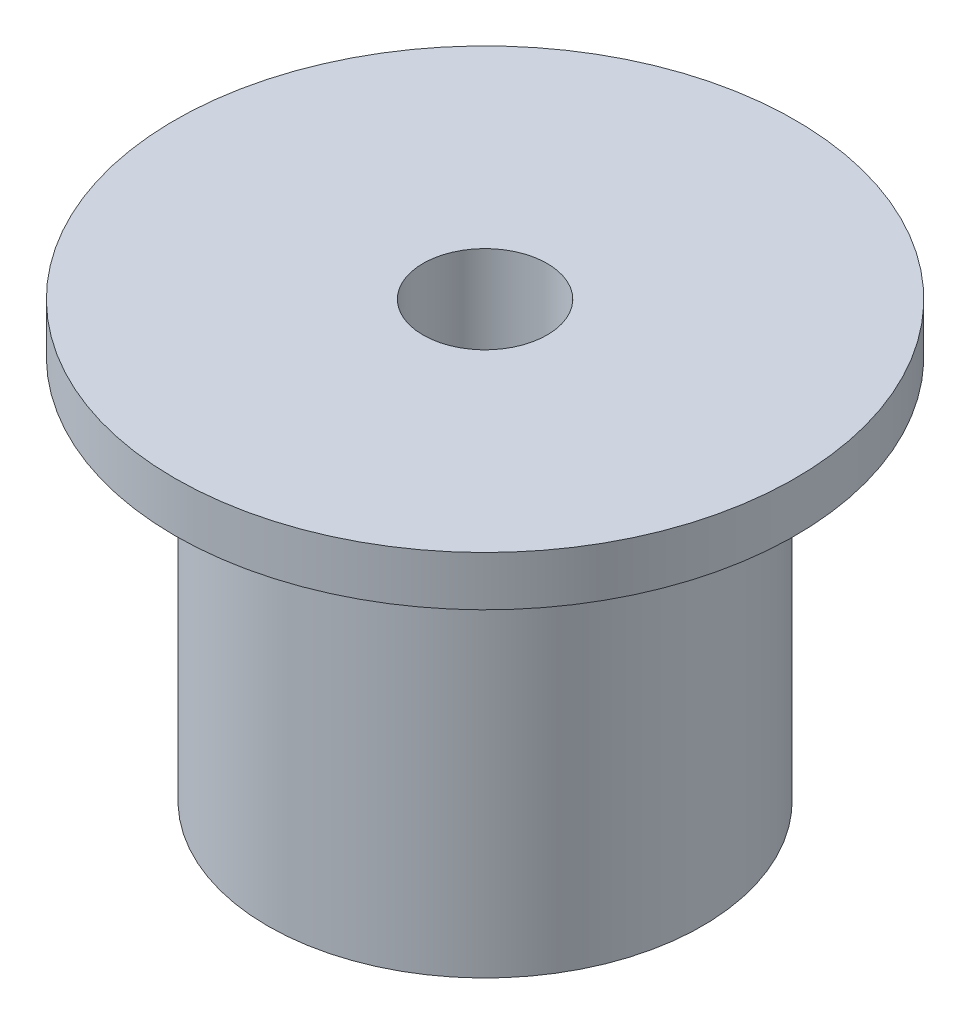
SolidWorks part; units mm, degrees
ref_plane "Front Plane" through (0, 0, 0) normal (0, 0, 1) x (1, 0, 0)
ref_plane "Top Plane" through (0, 0, 0) normal (0, 1, 0) x (1, 0, 0)
ref_plane "Right Plane" through (0, 0, 0) normal (1, 0, 0) x (0, 0, -1)
sketch "Sketch1" plane through (0, 0, 0) normal (0, 1, 0) x (1, 0, 0)
  circle A0 centre (0, 0) radius 11.1125
  dimension "D1" = 22.225
extrude "Boss-Extrude1" add sketch "Sketch1" along normal blind 22.225
sketch "Sketch2" plane through (0, 22.225, 0) normal (0, 1, 0) x (1, 0, 0)
  circle A0 centre (0, 0) radius 15.875
  dimension "D1" = 31.75
extrude "Boss-Extrude2" add sketch "Sketch2" against normal blind 2.54
hole_wizard "1/4 (0.25) Diameter Hole1" positions "Sketch3" profile "Sketch4" hole size "1/4" standard "ANSI Inch" end condition through all
sketch "Sketch3" plane through (0, 22.225, 0) normal (0, 1, 0) x (1, 0, 0)
  point P0 (0, 0)
sketch "Sketch4" plane through (0, 22.225, 0) normal (1, 0, 0) x (0, 0, 1)
  line L0 (0, 0) -> (0, 22.225)
  line L1 (0, 22.225) -> (3.175, 22.225)
  line L2 (3.175, 22.225) -> (3.175, 0)
  line L5 (3.175, 0) -> (0, 0)
  line L11 (0, -6.35) -> (0, 107.95) construction
  dimension "Thru Hole Dia." = 6.35
  dimension "Thru Hole Depth" = 22.225
